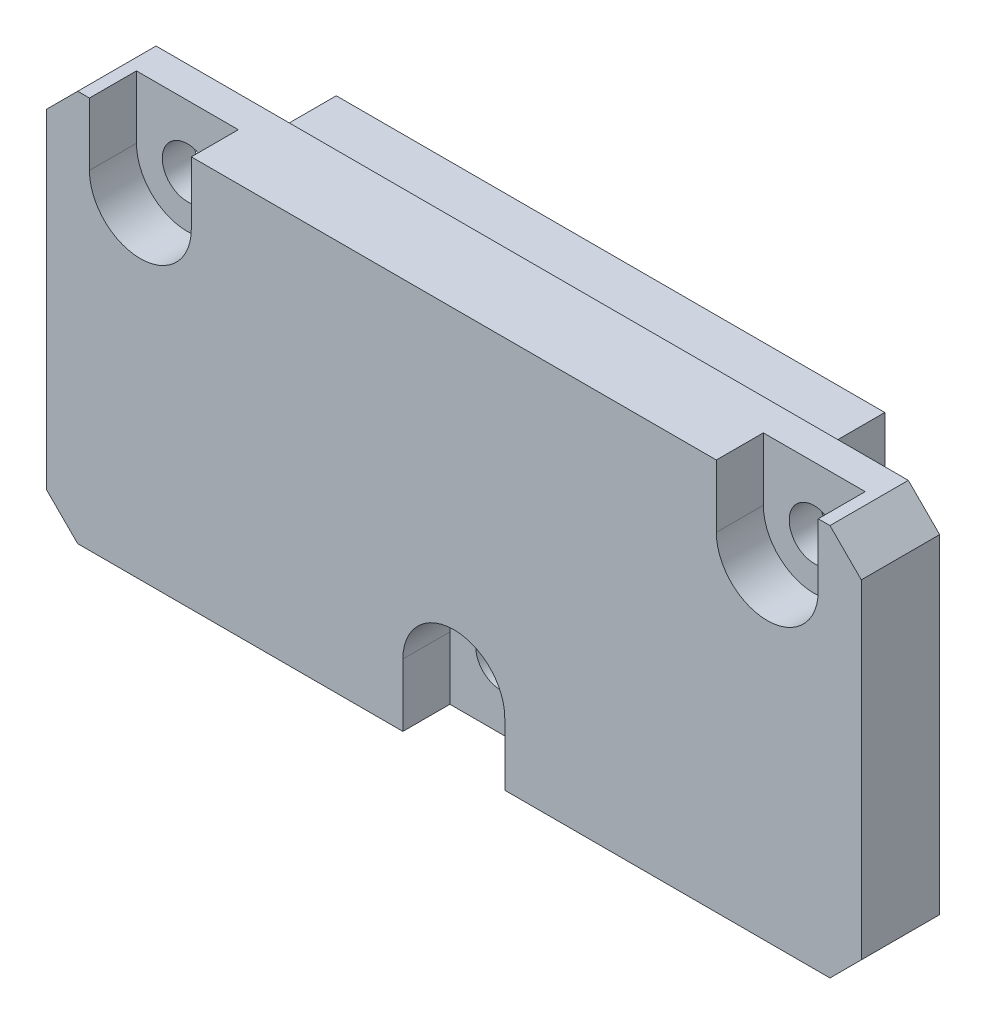
SolidWorks part; units mm, degrees
material "Сталь"
ref_plane "Спереди" through (0, 0, 0) normal (0, 0, 1) x (1, 0, 0)
ref_plane "Сверху" through (0, 0, 0) normal (0, 1, 0) x (1, 0, 0)
ref_plane "Справа" through (0, 0, 0) normal (1, 0, 0) x (0, 0, -1)
sketch "Эскиз1" plane through (0, 0, 0) normal (0, 0, 1) x (1, 0, 0)
  line L1 (-26, -12.5) -> (26, -12.5)
  line L2 (-26, -12.5) -> (-26, 12.5)
  line L3 (-26, 12.5) -> (26, 12.5)
  line L4 (26, -12.5) -> (26, 12.5)
  line L5 (-26, -12.5) -> (26, 12.5) construction
  line L6 (-26, 12.5) -> (26, -12.5) construction
  point P0 (0, 0)
  dimension "D1" = 52
  dimension "D2" = 25
extrude "Бобышка-Вытянуть1" add sketch "Эскиз1" along normal blind 5
chamfer "Фаска1" distance 2 angle 45 4 edges at (26, -12.5, 2.5) (-26, -12.5, 2.5) (-26, 12.5, 2.5) (26, 12.5, 2.5)
sketch "Эскиз2" plane through (0, 0, 0) normal (0, 0, -1) x (-1, 0, 0)
  line L0 (-17.5, 3) -> (17.5, 3) construction
  line L1 (-17.5, -4.5) -> (-17.5, 10.5) construction
  line L2 (17.5, 10.5) -> (17.5, -4.5) construction
  line L4 (17.5, -4.5) -> (-17.5, -4.5)
  line L5 (17.5, -4.5) -> (17.5, 10.5)
  line L6 (17.5, 10.5) -> (-17.5, 10.5)
  line L7 (-17.5, -4.5) -> (-17.5, 10.5)
  line L8 (17.5, -4.5) -> (-17.5, 10.5) construction
  line L9 (17.5, 10.5) -> (-17.5, -4.5) construction
  point P6 (0, 3)
extrude "Бобышка-Вытянуть2" add sketch "Эскиз2" along normal blind 5
sketch "Эскиз3" plane through (0, 0, 5) normal (0, 0, 1) x (1, 0, 0)
  line L0 (-24, -12.5) -> (24, -12.5) construction
  line L1 (-3.25, -8.5) -> (-3.25, -12.5)
  line L2 (-3.25, -12.5) -> (3.25, -12.5)
  line L3 (3.25, -12.5) -> (3.25, -8.5)
  line L4 (26, -10.5) -> (26, 10.5) construction
  line L5 (-26, 10.5) -> (-26, -10.5) construction
  line L6 (24, 12.5) -> (-24, 12.5) construction
  line L7 (-23.25, 8.5) -> (-23.25, 12.5)
  line L8 (-23.25, 12.5) -> (-16.75, 12.5)
  line L9 (-16.75, 12.5) -> (-16.75, 8.5)
  line L10 (16.75, 8.5) -> (16.75, 12.5)
  line L12 (23.25, 8.5) -> (23.25, 12.5)
  line L13 (23.25, 12.5) -> (16.75, 12.5)
  circle A0 centre (0, -8.5) radius 3.25
  circle A1 centre (-20, 8.5) radius 3.25
  circle A2 centre (20, 8.5) radius 3.25
  line M1 (-24, -12.5) -> (24, -12.5)
  line M5 (24, 12.5) -> (-24, 12.5)
  dimension "D1" = 6.5
  dimension "D2" = 4
  dimension "D3" = 6
  dimension "D4" = 6
  dimension "D5" = 4
extrude "Вырез-Вытянуть1" cut sketch "Эскиз3" against normal blind 3 contours A0 | A0 L1 L3 M1 | A1 L9 L7 M5 | A1 | A2 | A2 L12 L10 M5
sketch "Эскиз5" plane through (0, 0, 2) normal (0, 0, 1) x (1, 0, 0)
  circle A0 centre (0, -8.5) radius 1.6
  circle A1 centre (-20, 8.5) radius 1.6
  circle A2 centre (20, 8.5) radius 1.6
  dimension "D1" = 3.2
extrude "Вырез-Вытянуть2" cut sketch "Эскиз5" against normal through all
